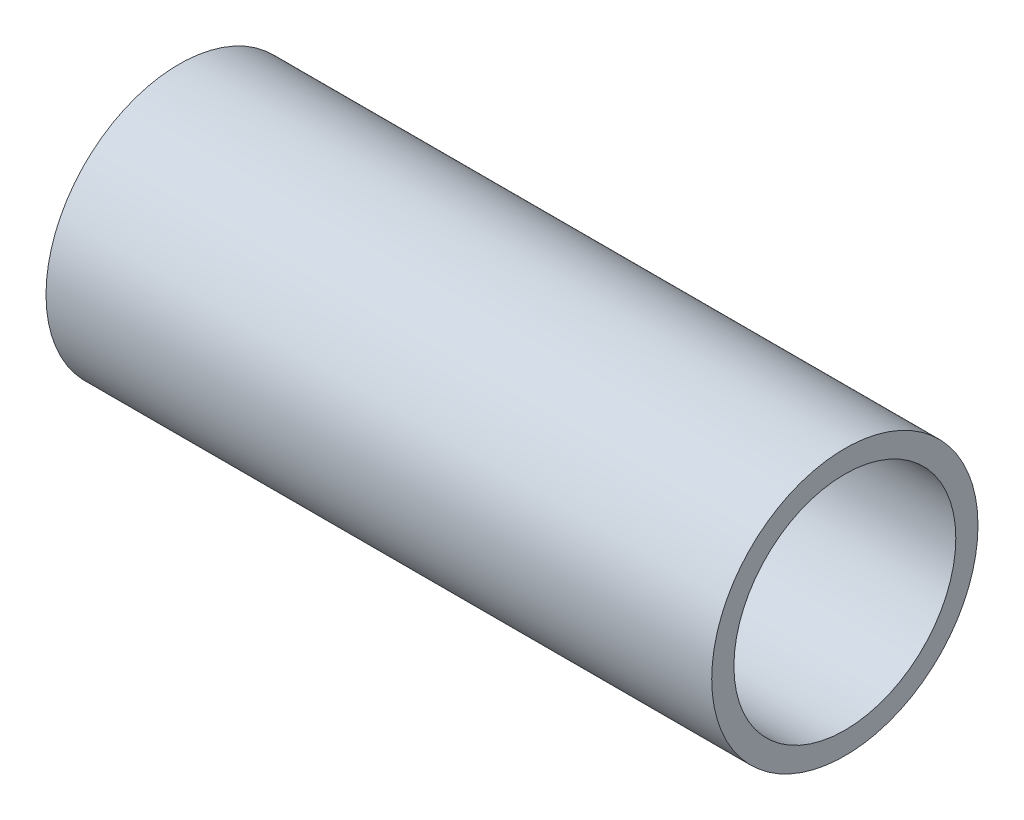
SolidWorks part; units mm, degrees
ref_plane "Front Plane" through (0, 0, 0) normal (0, 0, 1) x (1, 0, 0)
ref_plane "Top Plane" through (0, 0, 0) normal (0, 1, 0) x (1, 0, 0)
ref_plane "Right Plane" through (0, 0, 0) normal (1, 0, 0) x (0, 0, -1)
sketch "Sketch1" plane through (0, 0, 0) normal (0, 1, 0) x (1, 0, 0)
  line L0 (-26.9136, 0) -> (22.037, 0) construction
  line L1 (-8.7211, 0) -> (-8.7211, 3)
  line L2 (-8.7211, 3) -> (6.2789, 3)
  line L3 (6.2789, 3) -> (6.2789, 2.5)
  line L4 (6.2789, 2.5) -> (1.2789, 2.5)
  line L5 (1.2789, 2.5) -> (1.2789, 0)
  line L6 (-8.7211, 0) -> (1.2789, 0)
  dimension "D1" = 2.5
  dimension "D2" = 3
  dimension "D3" = 10
  dimension "D4" = 5
revolve "Revolve1" add sketch "Sketch1" angle 360 about L0
